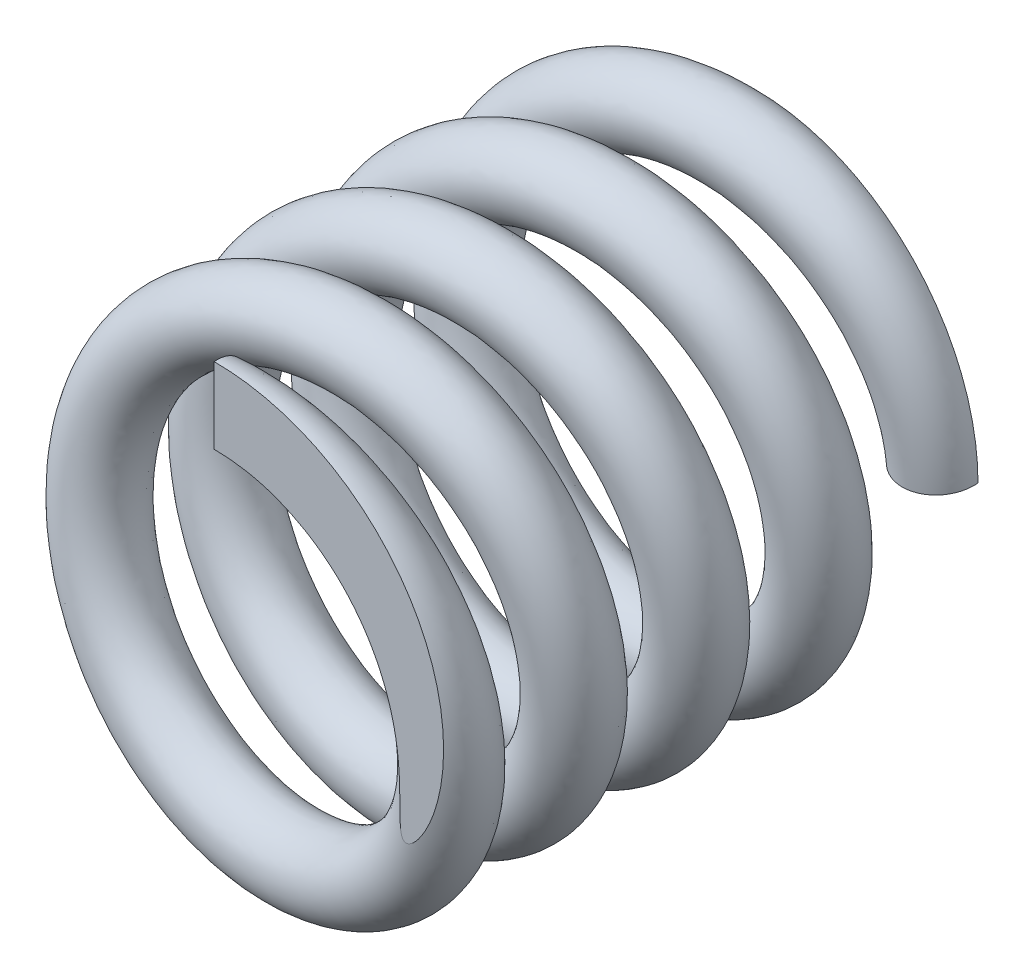
SolidWorks part; units mm, degrees
material "1.8519 (31CrMoV9)"
ref_plane "Front Plane" through (0, 0, 0) normal (0, 0, 1) x (1, 0, 0)
ref_plane "Top Plane" through (0, 0, 0) normal (0, 1, 0) x (1, 0, 0)
ref_plane "Right Plane" through (0, 0, 0) normal (1, 0, 0) x (0, 0, -1)
sketch "Sketch1" plane through (0, 0, 0) normal (0, 0, 1) x (1, 0, 0)
  circle A0 centre (0, 0) radius 6.7
  dimension "D1" = 13.4
curve "Helis/Spiral1" pitch 4 height 17 turns 4.25
ref_plane "Plane1" through (0, 6.7, 0) normal (0.9955, 0, -0.0946) x (-0.0946, 0, -0.9955)
sketch "Sketch3" plane through (0, 6.7, 0) normal (0.9955, 0, -0.0946) x (-0.0946, 0, -0.9955)
  circle A0 centre (0, 0.0172) radius 1.24
  dimension "D1" = 2.48
sweep "Sweep1" add profiles "Sketch3" path "Helis/Spiral1"
sketch "Sketch4" plane through (0, 0, 0) normal (0, 1, 0) x (1, 0, 0)
  line L0 (9.7126, 17) -> (-8.6759, 17)
  line L1 (-8.6759, 17) -> (-8.6759, 20.4903)
  line L2 (-8.6759, 20.4903) -> (9.7126, 20.4903)
  line L3 (9.7126, 20.4903) -> (9.7126, 17)
  line L4 (9.7126, 0) -> (9.7126, -3.1725)
  line L5 (9.7126, -3.1725) -> (-8.6759, -3.1725)
  line L6 (-8.6759, -3.1725) -> (-8.6759, 0)
  line L7 (-8.6759, 0) -> (9.7126, 0)
extrude "Cut-Extrude1" cut sketch "Sketch4" against normal through all both and the other way through all
